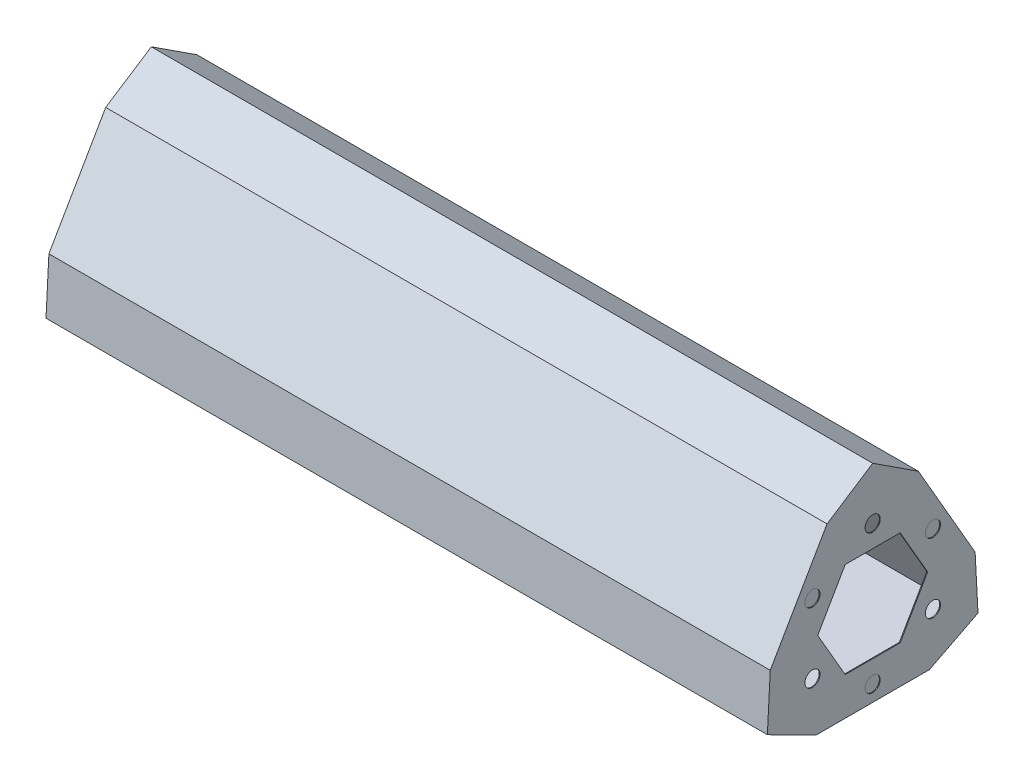
SolidWorks part; units mm, degrees
material "Polyethylene Cross-Linked"
ref_plane "Front Plane" through (0, 0, 0) normal (0, 0, 1) x (1, 0, 0)
ref_plane "Top Plane" through (0, 0, 0) normal (0, 1, 0) x (1, 0, 0)
ref_plane "Right Plane" through (0, 0, 0) normal (1, 0, 0) x (0, 0, -1)
sketch "Sketch1" plane through (0, 0, 0) normal (1, 0, 0) x (0, 0, -1)
  line L0 (0, 0) -> (44.5, 0)
  line L1 (0, 0) -> (22.25, 38.5381)
  line L2 (22.25, 38.5381) -> (44.5, 0)
  line L3 (0.6094, 11.4838) -> (12.6094, 32.2685)
  line L4 (12.6094, 32.2685) -> (22.25, 38.5381)
  line L5 (0.6094, 11.4838) -> (0, 0)
  line L6 (0, 0) -> (10.25, -5.2142)
  line L7 (10.25, -5.2142) -> (34.25, -5.2142)
  line L8 (34.25, -5.2142) -> (44.5, 0)
  line L9 (44.5, 0) -> (43.8906, 11.4838)
  line L10 (43.8906, 11.4838) -> (31.8906, 32.2685)
  line L11 (31.8906, 32.2685) -> (22.25, 38.5381)
  point P11 (-53.9608, 29.0314)
  point P13 (-52.9075, 30.4581)
  dimension "D2" = 44.5
  dimension "D4" = 60
  dimension "D5" = 60
  dimension "D6" = 24
  dimension "D7" = 11.5
extrude "Boss-Extrude1" add sketch "Sketch1" along normal blind 152.4 contours L10 L11 L2 L9 | L2 L1 L0 | L3 L5 L1 L4 | L7 L8 L0 L6
sketch "Sketch2" plane through (152.4, 0, 0) normal (1, 0, 0) x (0, 0, -1)
  line L0 (10.25, -5.2142) -> (34.25, -5.2142) construction
  line L1 (16.4417, 22.9063) -> (10.6335, 12.846)
  line L2 (10.6335, 12.846) -> (16.4417, 2.7858)
  line L3 (16.4417, 2.7858) -> (28.0583, 2.7858)
  line L4 (28.0583, 2.7858) -> (33.8665, 12.846)
  line L5 (33.8665, 12.846) -> (28.0583, 22.9063)
  line L6 (28.0583, 22.9063) -> (16.4417, 22.9063)
  line L7 (22.25, 38.5381) -> (22.25, -14.8896) construction
  line L9 (43.8906, 11.4838) -> (31.8906, 32.2685) construction
  circle A0 centre (22.25, 12.846) radius 10.0602 construction
  circle A1 centre (22.25, 27.5381) radius 1.6
  circle A7 centre (34.9737, 20.1921) radius 1.6
  circle A8 centre (34.9737, 5.5) radius 1.6
  circle A9 centre (22.25, -1.846) radius 1.6
  circle A10 centre (9.5263, 5.5) radius 1.6
  circle A11 centre (9.5263, 20.1921) radius 1.6
  dimension "D2" = 3.2
  dimension "D1" = 8
  dimension "D3" = 11
  dimension "D5" = 8
  dimension "D4" = 6
extrude "Cut-Extrude1" cut sketch "Sketch2" against normal blind 0.1778
sketch "Sketch4" plane through (152.2222, 0, 0) normal (1, 0, 0) x (0, 0, -1)
  line L4 (22.25, 22.9063) -> (22.25, 2.7858) construction
  line L5 (22.25, 36.0381) -> (2.1651, 1.25)
  line L6 (2.1651, 1.25) -> (42.3349, 1.25)
  line L7 (42.3349, 1.25) -> (22.25, 36.0381)
  line L8 (10.6335, 12.846) -> (33.3738, 12.846) construction
  line L9 (10.25, -5.2142) -> (34.25, -5.2142) construction
  line L13 (28.0583, 22.9063) -> (16.4417, 22.9063)
  line L14 (16.4417, 22.9063) -> (10.6335, 12.846)
  line L15 (10.6335, 12.846) -> (16.4417, 2.7858)
  line L16 (16.4417, 2.7858) -> (28.0583, 2.7858)
  line L17 (28.0583, 2.7858) -> (33.8665, 12.846)
  line L18 (33.8665, 12.846) -> (28.0583, 22.9063)
  line L19 (28.0583, 22.9063) -> (16.4417, 22.9063) construction
  line L20 (16.4417, 22.9063) -> (10.6335, 12.846) construction
  line L21 (10.6335, 12.846) -> (16.4417, 2.7858) construction
  line L22 (16.4417, 2.7858) -> (28.0583, 2.7858) construction
  line L23 (28.0583, 2.7858) -> (33.8665, 12.846) construction
  line L24 (33.8665, 12.846) -> (28.0583, 22.9063) construction
  circle A0 centre (22.25, 12.846) radius 11.596 construction
  point P13 (22.25, 12.846)
  dimension "D1" = 0
  dimension "D2" = 2.5
extrude "Cut-Extrude4" cut sketch "Sketch4" against normal offset from surface (152.0444 mm away) 0.1778 up to face at (0, 12.846, -22.25)
sketch "Sketch6" plane through (0, 0, 0) normal (-1, 0, 0) x (0, 0, 1)
  line L0 (-10.25, -5.2142) -> (-34.25, -5.2142) construction
  line L1 (-22.25, 22.661) -> (-30.75, 7.9386)
  line L2 (-30.75, 7.9386) -> (-13.75, 7.9386)
  line L3 (-13.75, 7.9386) -> (-22.25, 22.661)
  line L4 (-33.8665, 12.846) -> (-28.0583, 22.9063) construction
  line L5 (-28.0583, 2.7858) -> (-33.8665, 12.846) construction
  line L6 (-16.4417, 2.7858) -> (-28.0583, 2.7858) construction
  line L7 (-10.6335, 12.846) -> (-16.4417, 2.7858) construction
  line L8 (-16.4417, 22.9063) -> (-10.6335, 12.846) construction
  line L9 (-28.0583, 22.9063) -> (-16.4417, 22.9063) construction
  line L10 (-33.8665, 12.846) -> (-28.0583, 22.9063) construction
  line L11 (-28.0583, 2.7858) -> (-33.8665, 12.846) construction
  line L12 (-16.4417, 2.7858) -> (-28.0583, 2.7858) construction
  line L13 (-10.6335, 12.846) -> (-16.4417, 2.7858) construction
  line L14 (-16.4417, 22.9063) -> (-10.6335, 12.846) construction
  line L15 (-28.0583, 22.9063) -> (-16.4417, 22.9063) construction
  line L16 (-22.25, 22.9063) -> (-22.25, 2.7858) construction
  line L17 (-33.8665, 12.846) -> (-10.6335, 12.846) construction
  line L18 (-13.75, 7.9386) -> (-37.8906, 21.8761) construction
  line L19 (-43.8906, 11.4838) -> (-31.8906, 32.2685) construction
  circle A0 centre (-22.25, 12.846) radius 4.9075 construction
  circle A1 centre (-29.9641, 17.2998) radius 1.6
  circle A2 centre (-14.5359, 17.2998) radius 1.6
  circle A3 centre (-22.25, 3.9386) radius 1.6
  point P7 (-26.5, 15.2998)
  point P15 (-22.25, 12.846)
  dimension "D3" = 3.2
  dimension "D1" = 17
  dimension "D2" = 4
  dimension "D4" = 3
extrude "Cut-Extrude5" cut sketch "Sketch6" against normal up to surface (0.1778 mm away) up to face at (0.1778, 12.846, -22.25)
equation "\"HOLE_SIZE\"= 3.2mm"
equation "\"D3@Sketch6\"=\"HOLE_SIZE\""
equation "\"D2@Sketch2\"=\"HOLE_SIZE\""
